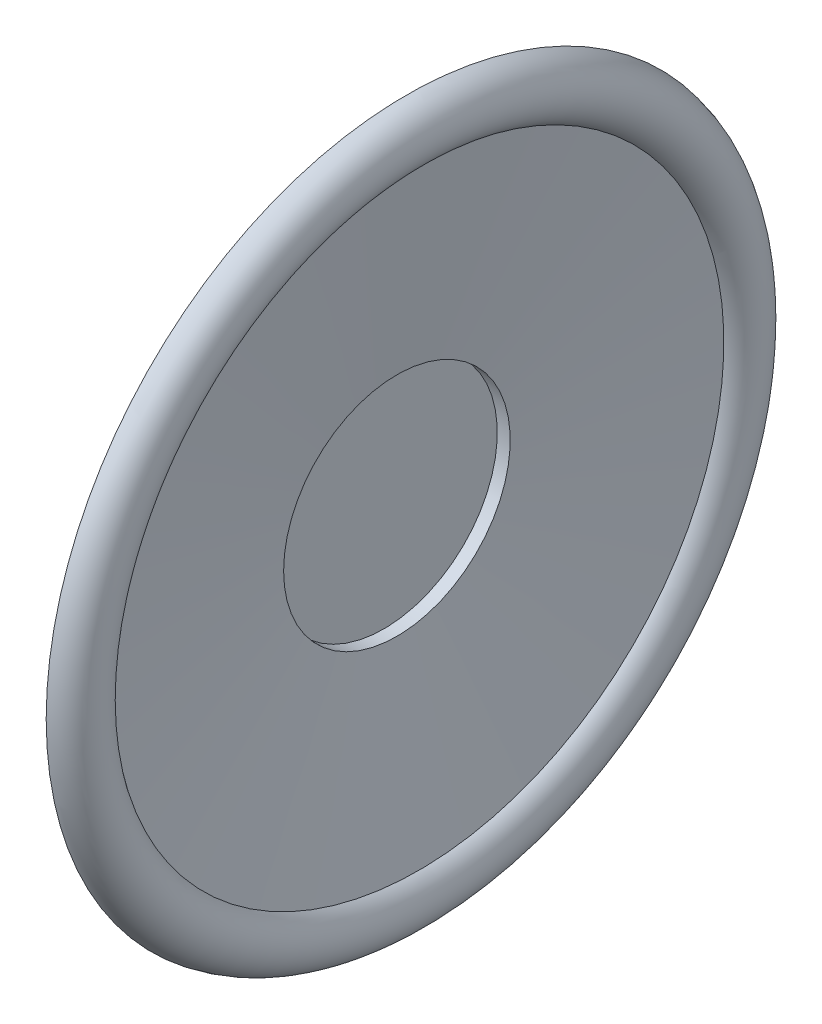
SolidWorks part; units mm, degrees
ref_plane "Front Plane" through (0, 0, 0) normal (0, 0, 1) x (1, 0, 0)
ref_plane "Top Plane" through (0, 0, 0) normal (0, 1, 0) x (1, 0, 0)
ref_plane "Right Plane" through (0, 0, 0) normal (1, 0, 0) x (0, 0, -1)
sketch "Sketch1" plane through (0, 0, 0) normal (0, 1, 0) x (1, 0, 0)
  line L0 (-0.7944, -7) -> (4.4022, -7) construction
  line L1 (0, 0) -> (1.1424, 9.9006)
  line L2 (0, 0) -> (-0.7944, 0)
  line L3 (-0.7944, 0) -> (-0.7944, -7)
  line L4 (1.3975, 12.112) -> (1.5, 13)
  line L5 (1.3975, 12.112) -> (1.2751, 11.0509)
  arc A2 (1.1424, 9.9006) -> (1.2787, 11.0818) centre (1.2105, 10.4912) ccw
  dimension "D1" = 1.5
  dimension "D2" = 20
  dimension "D3" = 7
revolve "Revolve-Thin3" add sketch "Sketch1" angle 360 about L0
